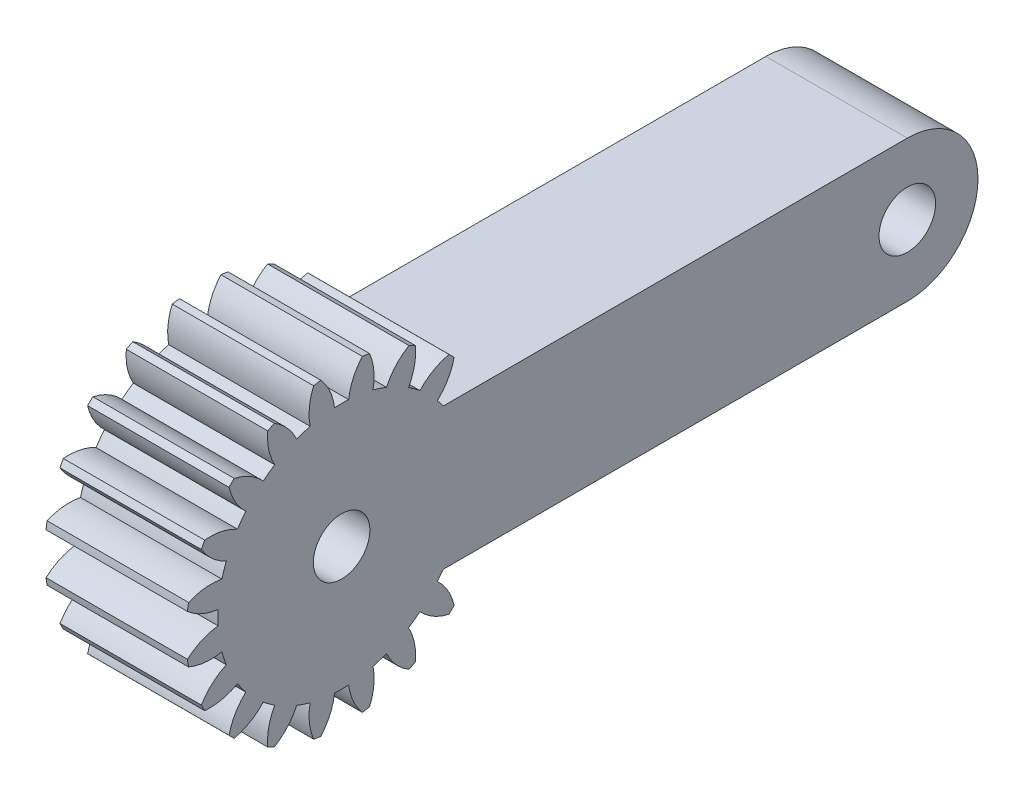
SolidWorks part; units mm, degrees
ref_plane "Plane1" through (0, 0, 0) normal (0, 0, 1) x (1, 0, 0)
ref_plane "Plane2" through (0, 0, 0) normal (0, 1, 0) x (1, 0, 0)
ref_plane "Plane3" through (0, 0, 0) normal (1, 0, 0) x (0, 0, -1)
sketch "HoldingSke" plane through (0, 0, 0) normal (0, 1, 0) x (1, 0, 0)
  line L0 (0, 0) -> (0.9397, -0.342)
  line L1 (-15, 0) -> (100, 0) construction
  line L2 (0, 0) -> (-2.1039, 2.3779)
  line L3 (0, 0) -> (-11.863, 4.5341)
  line L4 (0, 0) -> (8.1152, 2.9537)
  line L5 (0, 0) -> (-46.8476, -17.4728)
  line L6 (0, 0) -> (-8.2896, -5.593)
  line L7 (-2.1039, 2.3779) -> (8.6586, 51.2059)
  line L8 (-76.2, 54.61) -> (-76.1, 54.61)
  line L9 (-71.009, 38.7566) -> (-53.1078, 45.2721)
  line L10 (-76.2, 71.12) -> (104.1128, 71.12)
  line L11 (0, 0) -> (-10, 0)
  line L12 (-76.2, 101.6) -> (-76.162, 101.6)
  line L13 (24.9733, 27.94) -> (52.9518, 28.4284)
  line L14 (24.9733, 27.94) -> (24.9743, 27.94)
  line L15 (24.9733, 27.94) -> (100.4006, 29.5858)
  line L16 (-63.627, -1) -> (-12.827, -1)
  circle A0 centre (0, 0) radius 0.4
  circle A1 centre (0, 0) radius 8.749
  circle A2 centre (0, 0) radius 37.5
  circle A3 centre (0, 0) radius 0.4
  dimension "MHD" = 17.498
  dimension "Hub_dia" = 75
  dimension "Bore" = 0.8
  dimension "MBD" = 0.8
  dimension "Num_teeth" = 20
  dimension "Pitch" = 1
  dimension "Overall_len" = 50
  dimension "Show_teeth" = 20
  dimension "Thickness" = 10
  dimension "OAL" = 50.0001
  dimension "T_dim" = 0.1
  dimension "Ap" = 20
  dimension "H" = 19.05
  dimension "Pitch_radius" = 180.3128
  dimension "Width" = 10
  dimension "Backlash" = 0.038
  dimension "Addendum_fac" = 1
  dimension "Dedendum_fac" = 1.25
  dimension "Clearance_fac" = 0.25
  dimension "Dedendum_add" = 0.001
  dimension "Module" = 1
sketch "BasProSke" plane through (0, 0, 0) normal (0, 1, 0) x (1, 0, 0)
  line L0 (-10, 0) -> (60, 0) construction
  line L1 (0, 0) -> (0, 11)
  line L2 (0, 0) -> (10, 0)
  line L3 (10, 0) -> (10, 11)
  line L4 (10, 11) -> (0, 11)
  dimension "Thickness" = 10
  dimension "Diameter" = 22
revolve "Base-Revolve" add sketch "BasProSke" angle 360 about L0
sketch "TooCutSke" plane through (0, 0, 0) normal (1, 0, 0) x (0, 0, -1)
  line L1 (0, 0) -> (0, 107) construction
  line L2 (0, 0) -> (-0.8511, 9.9637) construction
  line L3 (0, 0) -> (-3.1206, 19.7028) construction
  line L4 (-0.8511, 9.9637) -> (-1.5603, 9.8514) construction
  arc A0 (0.4999, 8.7347) -> (-0.4999, 8.7347) centre (0, 0) ccw
  arc A1 (1.4852, 10.9249) -> (-1.4852, 10.9249) centre (0, 0) ccw
  circle A2 centre (0, 0) radius 10 construction
  circle A3 centre (0, 0) radius 9.3969 construction
  arc A4 (-0.4999, 8.7347) -> (-1.4852, 10.9249) centre (-4.4722, 8.2645) ccw
  arc A5 (1.4852, 10.9249) -> (0.4999, 8.7347) centre (4.4722, 8.2645) ccw
  dimension "Root_dia" = 17.498
  dimension "Overcut_dia" = 22.0508
  dimension "Pitch_dia" = 20
  dimension "Base_dia" = 18.7939
  dimension "Flank_rad" = 4
  dimension "Half_ang" = 9
  dimension "Half_CT" = 0.7181
extrude "ToothCut" cut sketch "TooCutSke" along normal through all
fillet "Breaks" [suppressed] radius 0.02
fillet "RootFillets" [suppressed] radius 0.251
pattern_circular "TeethCuts" count 20 every 18 about axis through (-10, 0, 0) along (1, 0, 0) of "ToothCut", "RootFillets", "Breaks"
sketch "HubNeaOneSke" plane through (0, 0, 0) normal (-1, 0, 0) x (0, 0, 1)
  circle A0 centre (0, 0) radius 8.749
  dimension "Diameter" = 17.498
extrude "HubNearOne" [suppressed] add sketch "HubNeaOneSke" along normal blind 40.0001
sketch "HubNeaBotSke" plane through (0, 0, 0) normal (-1, 0, 0) x (0, 0, 1)
  circle A0 centre (0, 0) radius 8.749
  dimension "Diameter" = 17.498
extrude "HubNearBoth" [suppressed] add sketch "HubNeaBotSke" along normal blind 20
ref_plane "FarPln" through (10, 0, 0) normal (1, 0, 0) x (0, 0, -1)
sketch "HubFarSke" plane through (10, 0, 0) normal (1, 0, 0) x (0, 0, -1)
  circle A0 centre (0, 0) radius 8.749
  dimension "Diameter" = 17.498
extrude "HubFar" [suppressed] add sketch "HubFarSke" along normal blind 20
sketch "BorSke" plane through (0, 0, 0) normal (1, 0, 0) x (0, 0, -1)
  circle A0 centre (0, 0) radius 0.4
  dimension "Diameter" = 0.8
extrude "Bore" cut sketch "BorSke" along normal mid plane 100.0001
sketch "KeySke" plane through (0, 0, 0) normal (1, 0, 0) x (0, 0, -1)
  line L0 (-0.05, 0) -> (-0.05, 0.5)
  line L1 (-0.05, 0.5) -> (0.05, 0.5)
  line L2 (0.05, 0.5) -> (0.05, 0)
  line L3 (0, 0) -> (0, 34) construction
  line L4 (-0.05, 0) -> (0.05, 0)
  dimension "Offset" = 0.5
  dimension "Width" = 0.1
extrude "Keyway" [suppressed] cut sketch "KeySke" along normal mid plane 100.0001
pattern_circular "Keyway2" [suppressed] count 2 every 90 about axis through (-10, 0, 0) along (1, 0, 0)
sketch "Croquis1" plane through (10, 0, 0) normal (1, 0, 0) x (0, 0, -1)
  line L0 (0, 0) -> (40, 0) construction
  line L1 (40, 5) -> (0, 5)
  line L2 (40, -5) -> (0, -5)
  arc A0 (0, 5) -> (0, -5) centre (0, 0) ccw
  circle A1 centre (0, 0) radius 2
  circle A2 centre (40, 0) radius 2
  arc A3 (40, -5) -> (40, 5) centre (40, 0) ccw
extrude "Saliente-Extruir1" add sketch "Croquis1" against normal blind 10
sketch "Croquis2" plane through (10, 0, 0) normal (1, 0, 0) x (0, 0, -1)
  circle A0 centre (0, 0) radius 2
extrude "Cortar-Extruir1" cut sketch "Croquis2" against normal blind 10
sketch "Croquis3" plane through (10, 0, 0) normal (1, 0, 0) x (0, 0, -1)
  line L0 (6.7727, 5.5386) -> (8.5152, 6.9636)
  line L1 (6.7727, -5.5386) -> (8.5152, -6.9636)
  line L2 (7.1795, 5) -> (9.798, 5)
  line L3 (7.1795, -5) -> (9.798, -5)
  arc A0 (7.1795, 5) -> (6.7727, 5.5386) centre (0, 0) ccw
  arc A1 (8.5152, -6.9636) -> (9.798, -5) centre (0, 0) ccw
  arc A2 (9.798, 5) -> (8.5152, 6.9636) centre (0, 0) ccw
  arc A3 (6.7727, -5.5386) -> (7.1795, -5) centre (0, 0) ccw
extrude "Cortar-Extruir2" cut sketch "Croquis3" against normal blind 10
equation "' \"Module@HoldingSke\" = 6.35"
equation "' \"Num_teeth@HoldingSke\" = 12"
equation "' \"Ap@HoldingSke\" =  20"
equation "' \"Ap@HoldingSke\" = 20"
equation "' \"Width@HoldingSke\" = 0.5 * 25.4"
equation "' \"Hub_dia@HoldingSke\"= 1 * 25.4"
equation "' \"Hub_dia@HoldingSke\" = 1 * 25.4"
equation "' \"Overall_len@HoldingSke\" = 1.0 * 25.4"
equation "' \"Bore@HoldingSke\" = 0.75 * 25.4"
equation "' \"T_dim@HoldingSke\" = 0.1 * 25.4"
equation "' \"Width@KeySke\" = 0.25 * 25.4"
equation "' \"Show_teeth@HoldingSke\" = 13"
equation "' \"Backlash@HoldingSke\" = 0.009 * 25.4"
equation "' \"Addendum_fac@HoldingSke\" = 1.0"
equation "' \"Dedendum_fac@HoldingSke\" = 1.25"
equation "' \"Dedendum_add@HoldingSke\" = 0.00005 * 25.4"
equation "' \"Clearance_fac@HoldingSke\" = 0.25"
equation "\"Pitch@HoldingSke\" = 1 / \"Module@HoldingSke\""
equation "\"Overcut_dia@TooCutSke\" = (\"Num_teeth@HoldingSke\" + 2 * \"Addendum_fac@HoldingSke\") / \"Pitch@HoldingSke\" + 0.002 * 25.4"
equation "\"Pitch_dia@TooCutSke\" = \"Num_teeth@HoldingSke\" / \"Pitch@HoldingSke\""
equation "\"Base_dia@TooCutSke\" = \"Num_teeth@HoldingSke\" / \"Pitch@HoldingSke\" * cos((\"Ap@HoldingSke\"  * 3.14159265 / 180))"
equation "\"Root_dia@TooCutSke\" = (\"Num_teeth@HoldingSke\" + 2) / \"Pitch@HoldingSke\" - 2 * (\"Addendum_fac@HoldingSke\" + \"Dedendum_fac@HoldingSke\") / \"Pitch@HoldingSke\" - \"Dedendum_add@HoldingSke\" * 2"
equation "\"Half_ang@TooCutSke\" = 180 / \"Num_teeth@HoldingSke\""
equation "\"Half_CT@TooCutSke\" = \"Num_teeth@HoldingSke\" / \"Pitch@HoldingSke\" * sin((3.14159265 / 2 / \"Num_teeth@HoldingSke\")) / 2 - 7 * \"Backlash@HoldingSke\" / 4"
equation "\"Flank_rad@TooCutSke\" = \"Num_teeth@HoldingSke\" / \"Pitch@HoldingSke\" / 5"
equation "\"Radius@RootFillets\" = \"Clearance_fac@HoldingSke\" / \"Pitch@HoldingSke\" + \"Dedendum_add@HoldingSke\""
equation "\"Break_rad@Breaks\" = 0.02 / \"Pitch@HoldingSke\""
equation "\"Thickness@HoldingSke\" = \"Width@HoldingSke\""
equation "\"OAL@HoldingSke\" = \"Thickness@HoldingSke\""
equation "\"MHD@HoldingSke\" = (\"Num_teeth@HoldingSke\" + 2) / \"Pitch@HoldingSke\" - 2 * (\"Addendum_fac@HoldingSke\" + \"Dedendum_fac@HoldingSke\")  / \"Pitch@HoldingSke\" - \"Dedendum_add@HoldingSke\" * 2"
equation "\"MBD@HoldingSke\" = (\"Num_teeth@HoldingSke\" + 2) / \"Pitch@HoldingSke\" - 2 * (\"Addendum_fac@HoldingSke\" + \"Dedendum_fac@HoldingSke\")  / \"Pitch@HoldingSke\" - \"Dedendum_add@HoldingSke\" * 2 - 0.002 * 25.4"
equation "\"MHD@HoldingSke\" = ((sgn( \"MHD@HoldingSke\" - \"Hub_dia@HoldingSke\" )-1)*( \"MHD@HoldingSke\" - \"Hub_dia@HoldingSke\" ))/-2+ \"Hub_dia@HoldingSke\""
equation "\"MBD@HoldingSke\" = ((sgn( \"MBD@HoldingSke\" - \"Bore@HoldingSke\" )-1)*( \"MBD@HoldingSke\" - \"Bore@HoldingSke\" ))/-2+ \"Bore@HoldingSke\""
equation "\"OAL@HoldingSke\" = ((sgn( \"OAL@HoldingSke\" - \"Overall_len@HoldingSke\" )+1)*( \"OAL@HoldingSke\" - \"Overall_len@HoldingSke\" ))/2 + \"Overall_len@HoldingSke\" + 0.000002 * 25.4"
equation "\"Num_teeth@TeethCuts\" = int( \"Show_teeth@HoldingSke\" ) + 1"
equation "\"Num_teeth@TeethCuts\" = ((sgn( \"Num_teeth@TeethCuts\" - \"Num_teeth@HoldingSke\" )-1)*( \"Num_teeth@TeethCuts\" - \"Num_teeth@HoldingSke\" ))/-2+ \"Num_teeth@HoldingSke\""
equation "\"Num_teeth@TeethCuts\" = ((sgn( \"Num_teeth@TeethCuts\" - 2.0)+1)*( \"Num_teeth@TeethCuts\" - 2.0))/2 +2.0"
equation "\"Angle@TeethCuts\" = 360.0 / \"Num_teeth@HoldingSke\""
equation "\"Diameter@BasProSke\" = (\"Num_teeth@HoldingSke\" + 2 * \"Addendum_fac@HoldingSke\") / \"Pitch@HoldingSke\""
equation "\"Thickness@BasProSke\"  = \"Thickness@HoldingSke\""
equation "' \"Fillet_rad@BasProSke\" =  \"Thickness@HoldingSke\" * 0.05"
equation "' \"Fillet_rad@BasProSke\" = \"Thickness@HoldingSke\" * 0.05"
equation "\"MHD@HoldingSke\" = ((sgn( \"MHD@HoldingSke\" - \"Root_dia@TooCutSke\" )-1)*( \"MHD@HoldingSke\" - \"Root_dia@TooCutSke\" ))/-2+ \"Root_dia@TooCutSke\""
equation "\"Diameter@HubNeaOneSke\" = \"MHD@HoldingSke\""
equation "\"Length@HubNearOne\" = \"OAL@HoldingSke\" - \"Thickness@BasProSke\""
equation "\"Diameter@HubNeaBotSke\" = \"MHD@HoldingSke\""
equation "\"Length@HubNearBoth\" = ( \"OAL@HoldingSke\" - \"Thickness@BasProSke\" ) / 2.0"
equation "\"Thickness@FarPln\" = \"Thickness@BasProSke\""
equation "\"Diameter@HubFarSke\" = \"MHD@HoldingSke\""
equation "\"Length@HubFar\" = ( \"OAL@HoldingSke\" - \"Thickness@BasProSke\" ) / 2.0"
equation "\"Diameter@BorSke\" = \"MBD@HoldingSke\""
equation "\"D1@Bore\" = \"OAL@HoldingSke\" * 2.0"
equation "\"D1@Keyway\" = \"OAL@HoldingSke\" * 2.0"
equation "\"Offset@KeySke\" = \"T_dim@HoldingSke\" + \"MBD@HoldingSke\" / 2.0"
